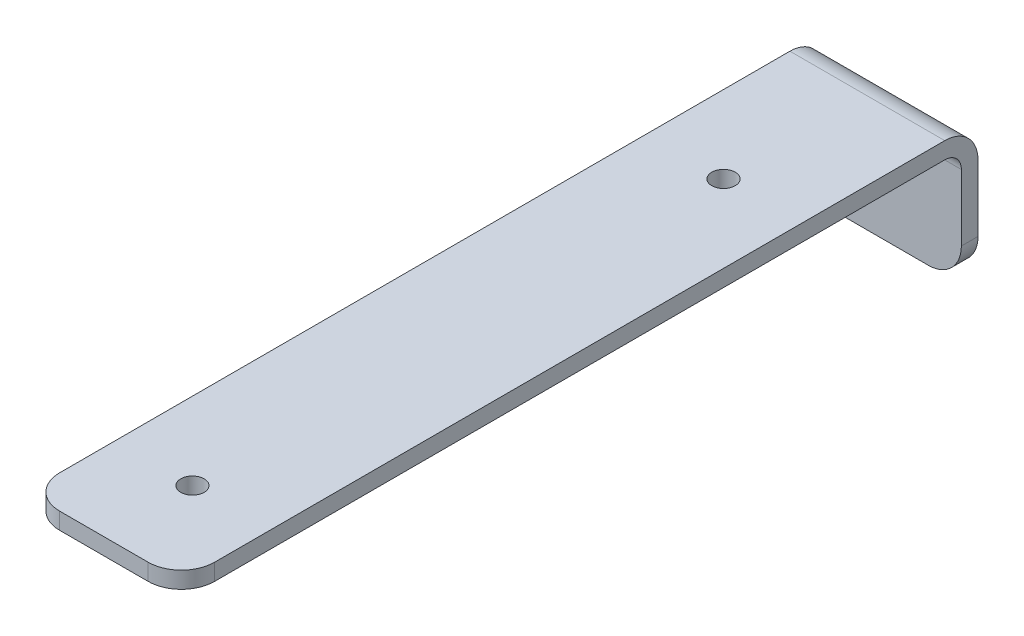
SolidWorks part; units mm, degrees
material "Plain Carbon Steel"
ref_plane "Front Plane" through (0, 0, 0) normal (0, 0, 1) x (1, 0, 0)
ref_plane "Top Plane" through (0, 0, 0) normal (0, 1, 0) x (1, 0, 0)
ref_plane "Right Plane" through (0, 0, 0) normal (1, 0, 0) x (0, 0, -1)
sketch "Sketch1" plane through (0, 0, 0) normal (1, 0, 0) x (0, 0, -1)
  line L0 (0, 0) -> (0, 33.3248)
  line L1 (0, 33.3248) -> (-223.8248, 33.3248)
  line L2 (-223.8248, 33.3248) -> (-223.8248, 38.1)
  line L3 (-223.8248, 38.1) -> (4.7752, 38.1)
  line L4 (4.7752, 38.1) -> (4.7752, 0)
  line L5 (4.7752, 0) -> (0, 0)
  dimension "D1" = 38.1
  dimension "D2" = 228.6
  dimension "D3" = 4.7752
extrude "Boss-Extrude1" add sketch "Sketch1" along normal blind 44.45
fillet "Fillet1" radius 4.7752 1 edges at (22.225, 33.3248, 0)
fillet "Fillet2" radius 9.525 1 edges at (22.225, 38.1, -4.7752)
fillet "Fillet3" radius 9.525 4 edges at (0, 0, -2.3876) (44.45, 0, -2.3876) (0, 35.7124, 223.8248) (44.45, 35.7124, 223.8248)
sketch "Sketch2" plane through (0, 38.1, 0) normal (0, 1, 0) x (1, 0, 0)
  line L0 (0, 4.7752) -> (44.45, 4.7752) construction
  line L1 (44.45, -4.7498) -> (44.45, -214.2998) construction
  circle A0 centre (22.225, -198.4248) radius 3.3655
  circle A1 centre (22.225, -46.0248) radius 3.3655
  dimension "D1" = 6.731
  dimension "D2" = 50.8
  dimension "D3" = 152.4
  dimension "D4" = 22.225
extrude "Cut-Extrude1" cut sketch "Sketch2" against normal through all
